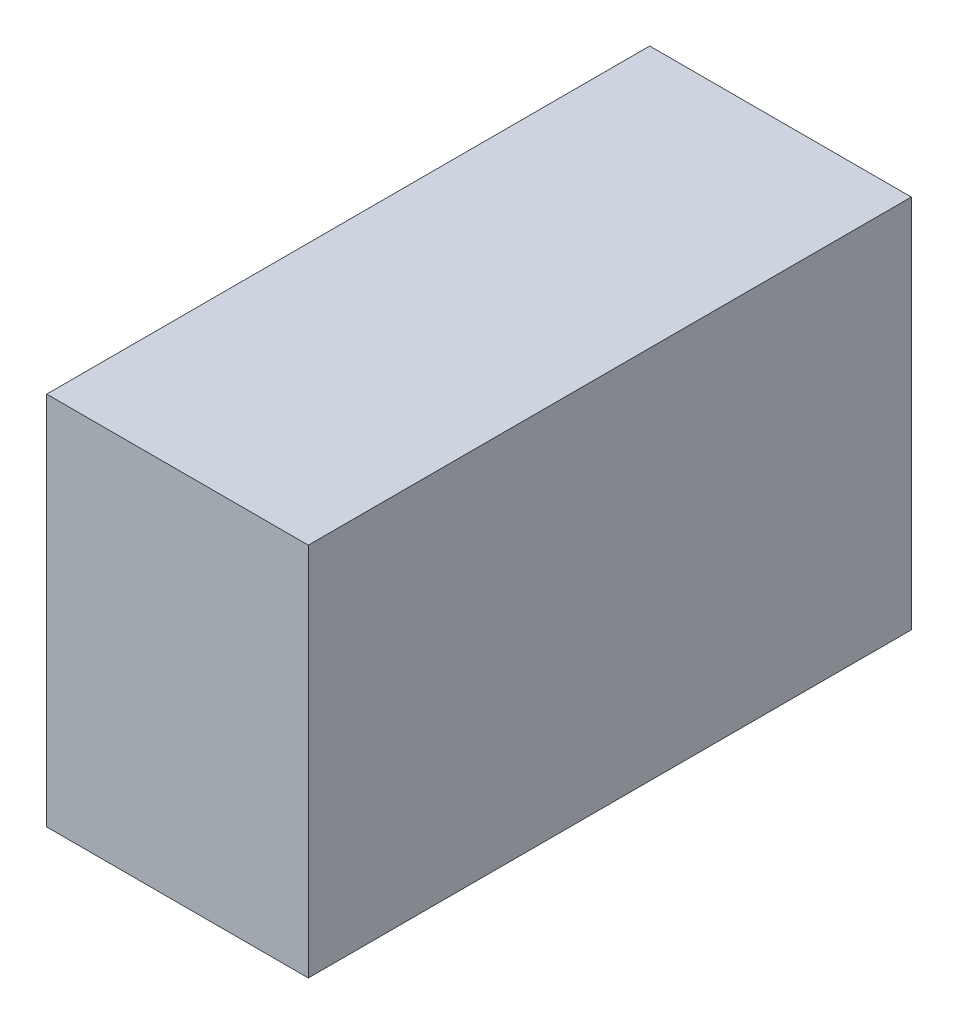
SolidWorks part; units mm, degrees
ref_plane "Front Plane" through (0, 0, 0) normal (0, 0, 1) x (1, 0, 0)
ref_plane "Top Plane" through (0, 0, 0) normal (0, 1, 0) x (1, 0, 0)
ref_plane "Right Plane" through (0, 0, 0) normal (1, 0, 0) x (0, 0, -1)
sketch "Sketch1" plane through (0, 0, 0) normal (0, 1, 0) x (1, 0, 0)
  line L1 (-32.8, -75.6) -> (32.8, -75.6)
  line L2 (-32.8, -75.6) -> (-32.8, 75.6)
  line L3 (-32.8, 75.6) -> (32.8, 75.6)
  line L4 (32.8, -75.6) -> (32.8, 75.6)
  line L5 (-32.8, -75.6) -> (32.8, 75.6) construction
  line L6 (-32.8, 75.6) -> (32.8, -75.6) construction
  point P0 (0, 0)
  dimension "D1" = 151.2
  dimension "D2" = 65.6
extrude "Boss-Extrude1" add sketch "Sketch1" along normal blind 94
